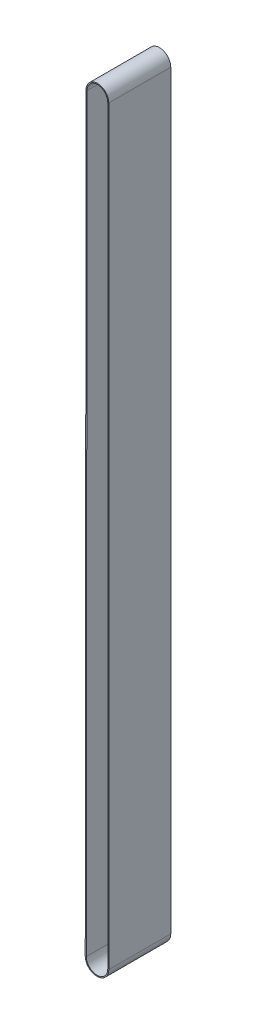
SolidWorks part; units mm, degrees
ref_plane "Front Plane" through (0, 0, 0) normal (0, 0, 1) x (1, 0, 0)
ref_plane "Top Plane" through (0, 0, 0) normal (0, 1, 0) x (1, 0, 0)
ref_plane "Right Plane" through (0, 0, 0) normal (1, 0, 0) x (0, 0, -1)
sketch "Sketch1" plane through (0, 0, 0) normal (0, 0, 1) x (1, 0, 0)
  line L0 (-96, 3595) -> (-103.9999, -3669.8855)
  line L1 (104, -3670) -> (104, 3595)
  circle A0 centre (4, 3595) radius 100 construction
  arc A1 (104, 3595) -> (-96, 3595) centre (4, 3595) ccw
  arc A5 (-103.9999, -3669.8855) -> (104, -3670) centre (0, -3670) ccw
  point P4 (0, -3905)
  point P5 (0, -3670)
extrude "Extrude-Thin3" add sketch "Sketch1" along normal mid plane 600 thin
